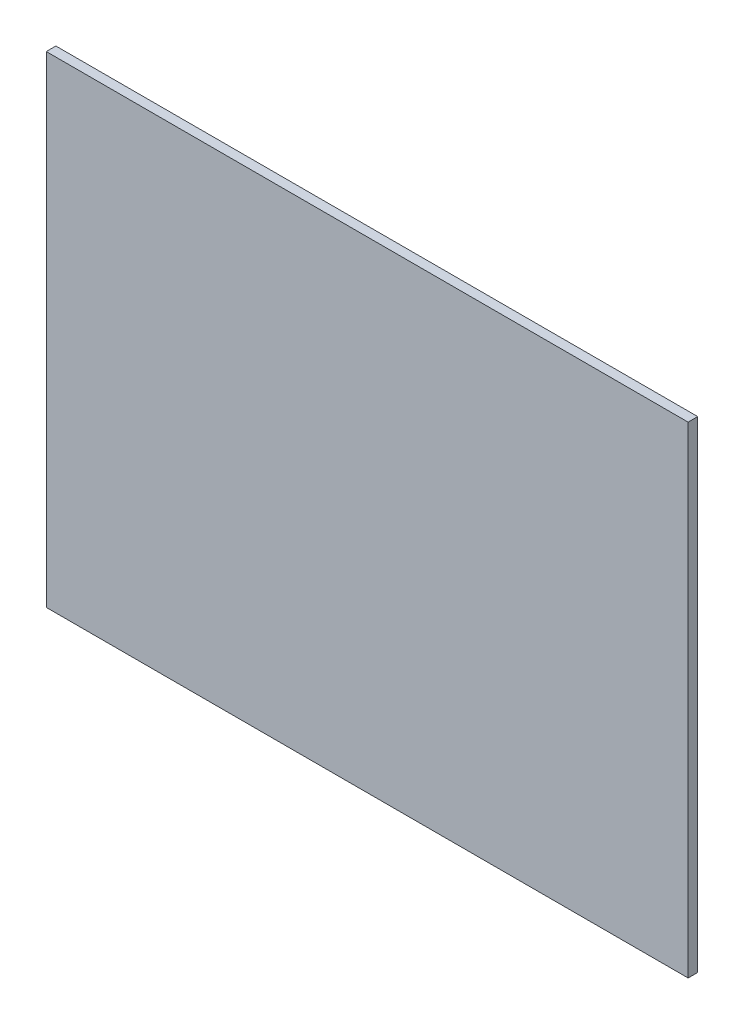
SolidWorks part; units mm, degrees
material "Cedar"
ref_plane "Front Plane" through (0, 0, 0) normal (0, 0, 1) x (1, 0, 0)
ref_plane "Top Plane" through (0, 0, 0) normal (0, 1, 0) x (1, 0, 0)
ref_plane "Right Plane" through (0, 0, 0) normal (1, 0, 0) x (0, 0, -1)
sketch "Sketch1" plane through (0, 0, 0) normal (0, 0, 1) x (1, 0, 0)
  line L1 (-609.6, -457.2) -> (609.6, -457.2)
  line L2 (-609.6, -457.2) -> (-609.6, 457.2)
  line L3 (-609.6, 457.2) -> (609.6, 457.2)
  line L4 (609.6, -457.2) -> (609.6, 457.2)
  line L5 (-609.6, -457.2) -> (609.6, 457.2) construction
  line L6 (-609.6, 457.2) -> (609.6, -457.2) construction
  point P0 (0, 0)
  dimension "D1" = 1219.2
  dimension "D2" = 914.4
extrude "Boss-Extrude1" add sketch "Sketch1" along normal blind 18.2562
